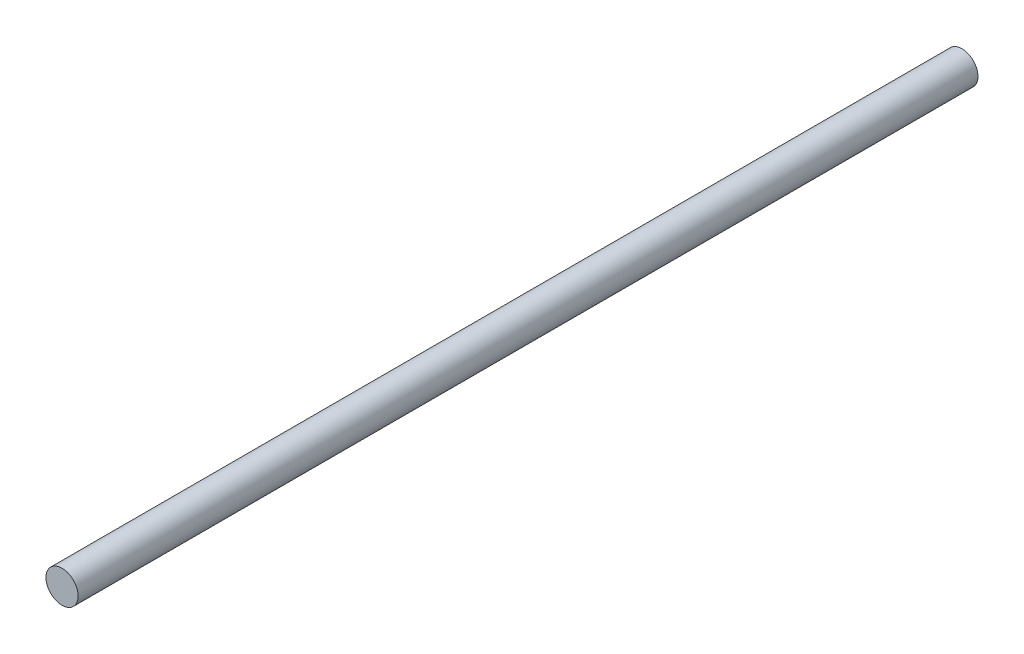
SolidWorks part; units mm, degrees
ref_plane "Front Plane" through (0, 0, 0) normal (0, 0, 1) x (1, 0, 0)
ref_plane "Top Plane" through (0, 0, 0) normal (0, 1, 0) x (1, 0, 0)
ref_plane "Right Plane" through (0, 0, 0) normal (1, 0, 0) x (0, 0, -1)
sketch "Sketch1" plane through (0, 0, 0) normal (0, 0, 1) x (1, 0, 0)
  circle A0 centre (0, 0) radius 3.175
  dimension "D1" = 6.35
extrude "Boss-Extrude1" add sketch "Sketch1" along normal blind 177.8
